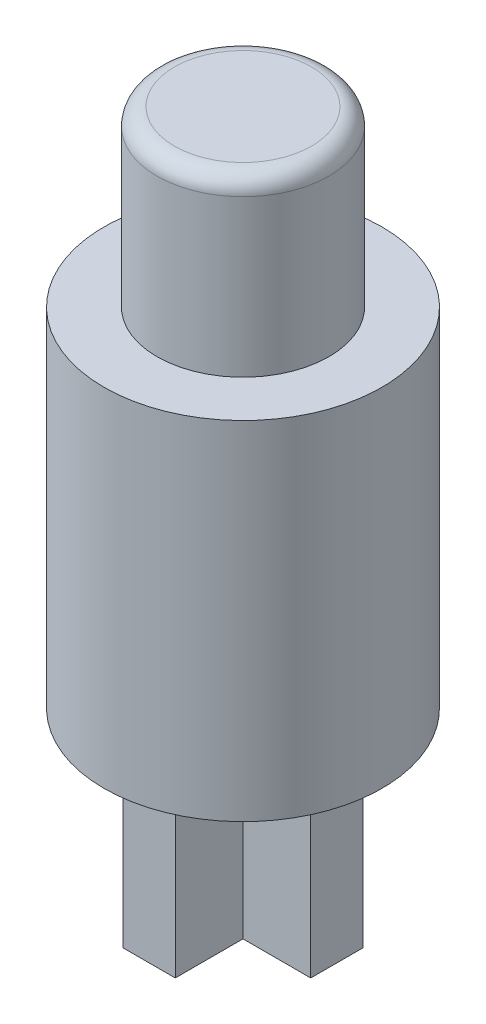
SolidWorks part; units mm, degrees
ref_plane "Front Plane" through (0, 0, 0) normal (0, 0, 1) x (1, 0, 0)
ref_plane "Top Plane" through (0, 0, 0) normal (0, 1, 0) x (1, 0, 0)
ref_plane "Right Plane" through (0, 0, 0) normal (1, 0, 0) x (0, 0, -1)
sketch "Sketch1" plane through (0, 0, 0) normal (0, 1, 0) x (1, 0, 0)
  circle A0 centre (0, 0) radius 4
  dimension "D1" = 8
extrude "Boss-Extrude1" add sketch "Sketch1" against normal blind 10
sketch "Sketch2" plane through (0, 0, 0) normal (0, 1, 0) x (1, 0, 0)
  circle A0 centre (0, 0) radius 2.475
  dimension "D1" = 4.95
extrude "Boss-Extrude2" add sketch "Sketch2" along normal blind 5
sketch "Sketch3" plane through (0, -10, 0) normal (0, -1, 0) x (1, 0, 0)
  line L1 (-0.75, 2.7) -> (0.75, 2.7)
  line L2 (-0.75, 2.7) -> (-0.75, -2.7)
  line L3 (-0.75, -2.7) -> (0.75, -2.7)
  line L4 (0.75, 2.7) -> (0.75, -2.7)
  line L5 (-0.75, 2.7) -> (0.75, -2.7) construction
  line L6 (-0.75, -2.7) -> (0.75, 2.7) construction
  line L7 (-2.7, 0.75) -> (2.7, 0.75)
  line L8 (-2.7, 0.75) -> (-2.7, -0.75)
  line L9 (-2.7, -0.75) -> (2.7, -0.75)
  line L10 (2.7, 0.75) -> (2.7, -0.75)
  line L11 (-2.7, 0.75) -> (2.7, -0.75) construction
  line L12 (-2.7, -0.75) -> (2.7, 0.75) construction
  point P0 (0, 0)
  point P7 (0, 0)
  dimension "D1" = 1.5
  dimension "D2" = 1.5
  dimension "D3" = 5.4
  dimension "D4" = 5.4
extrude "Boss-Extrude3" add sketch "Sketch3" along normal blind 5 contours L1 L4 L3 L2 | L8 L9 L10 L7
fillet "Fillet3" radius 0.5 1 edges at (0, 5, 2.475)
